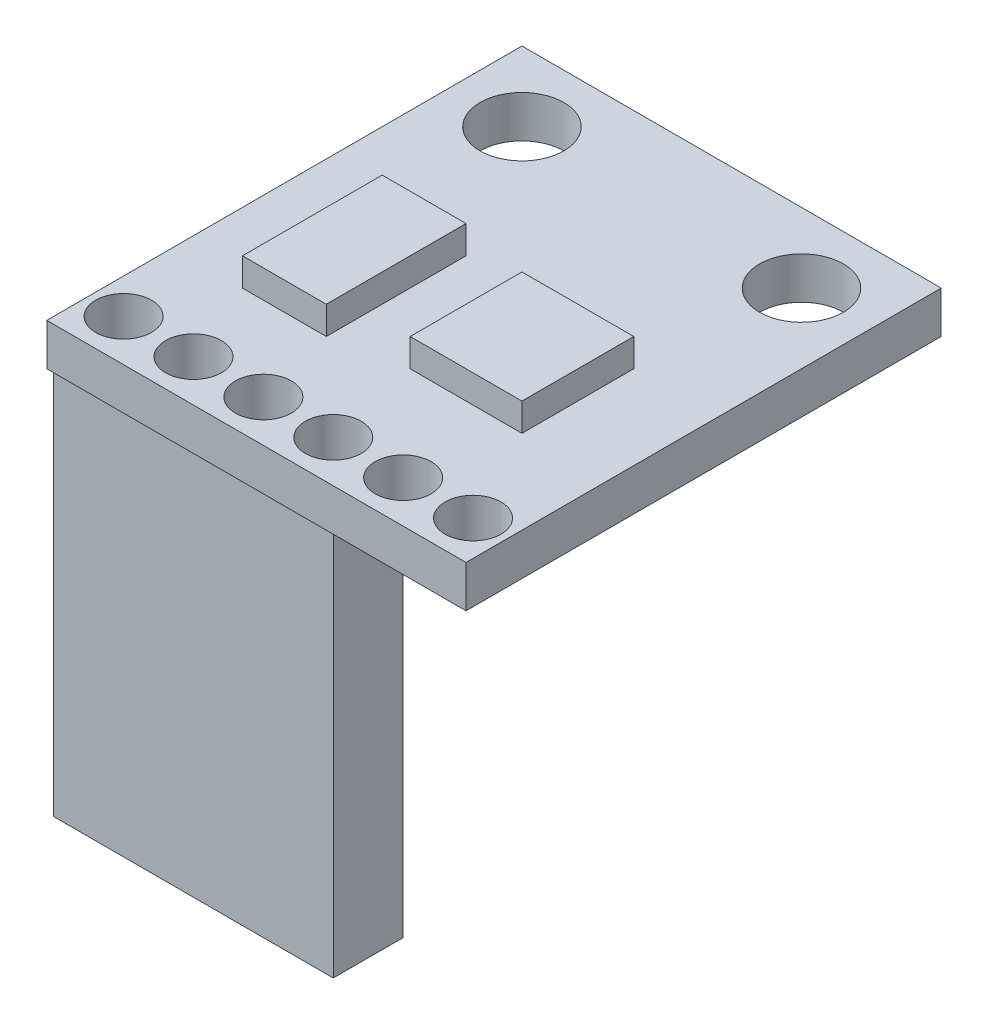
SolidWorks part; units mm, degrees
ref_plane "Plan de face" through (0, 0, 0) normal (0, 0, 1) x (1, 0, 0)
ref_plane "Plan de dessus" through (0, 0, 0) normal (0, 1, 0) x (1, 0, 0)
ref_plane "Plan de droite" through (0, 0, 0) normal (1, 0, 0) x (0, 0, -1)
sketch "Esquisse1" plane through (0, 0, 0) normal (0, 1, 0) x (1, 0, 0)
  line L1 (-7.5, 8.5) -> (7.5, 8.5)
  line L2 (-7.5, 8.5) -> (-7.5, -8.5)
  line L3 (-7.5, -8.5) -> (7.5, -8.5)
  line L4 (7.5, 8.5) -> (7.5, -8.5)
  circle A0 centre (-5, 6) radius 1.5
  circle A1 centre (5, 6) radius 1.5
  circle A2 centre (-6.25, -7) radius 1
  circle A3 centre (-3.75, -7) radius 1
  circle A4 centre (-1.25, -7) radius 1
  circle A5 centre (1.25, -7) radius 1
  circle A6 centre (3.75, -7) radius 1
  circle A7 centre (6.25, -7) radius 1
  dimension "D8" = 3
  dimension "D10" = 3
  dimension "D13" = 2
  dimension "D1" = 15
  dimension "D2" = 17
  dimension "D3" = 7.5
  dimension "D4" = 8.5
  dimension "D5" = 5
  dimension "D6" = 10
  dimension "D7" = 2.5
  dimension "D9" = 2.5
  dimension "D11" = 1.5
  dimension "D12" = 1.25
  dimension "D14" = 6
extrude "Boss.-Extru.1" add sketch "Esquisse1" along normal blind 1.5
sketch "Esquisse2" plane through (0, 1.5, 0) normal (0, 1, 0) x (1, 0, 0)
  line L0 (-7.5, 8.5) -> (-7.5, -8.5) construction
  line L1 (-5, 1) -> (-2, 1)
  line L2 (-5, 1) -> (-5, -4)
  line L3 (-5, -4) -> (-2, -4)
  line L4 (-2, 1) -> (-2, -4)
  line L5 (0.5, 0.5) -> (4.5, 0.5)
  line L6 (0.5, 0.5) -> (0.5, -3.5)
  line L7 (0.5, -3.5) -> (4.5, -3.5)
  line L8 (4.5, 0.5) -> (4.5, -3.5)
  line L9 (7.5, 8.5) -> (-7.5, 8.5) construction
  line L10 (7.5, -8.5) -> (7.5, 8.5) construction
  dimension "D1" = 3
  dimension "D2" = 5
  dimension "D3" = 4
  dimension "D4" = 4
  dimension "D5" = 2.5
  dimension "D6" = 7.5
  dimension "D7" = 3
  dimension "D8" = 8
extrude "Boss.-Extru.2" add sketch "Esquisse2" along normal blind 1
sketch "Esquisse3" plane through (0, 0, 0) normal (0, -1, 0) x (1, 0, 0)
  line L0 (-7.5, 8.5) -> (7.5, 8.5) construction
  line L1 (-7.5, 8.25) -> (2.5, 8.25)
  line L2 (-7.5, 8.25) -> (-7.5, 5.75)
  line L3 (-7.5, 5.75) -> (2.5, 5.75)
  line L4 (2.5, 8.25) -> (2.5, 5.75)
  dimension "D1" = 2.5
  dimension "D2" = 10
  dimension "D3" = 0.25
extrude "Boss.-Extru.3" add sketch "Esquisse3" along normal blind 14
